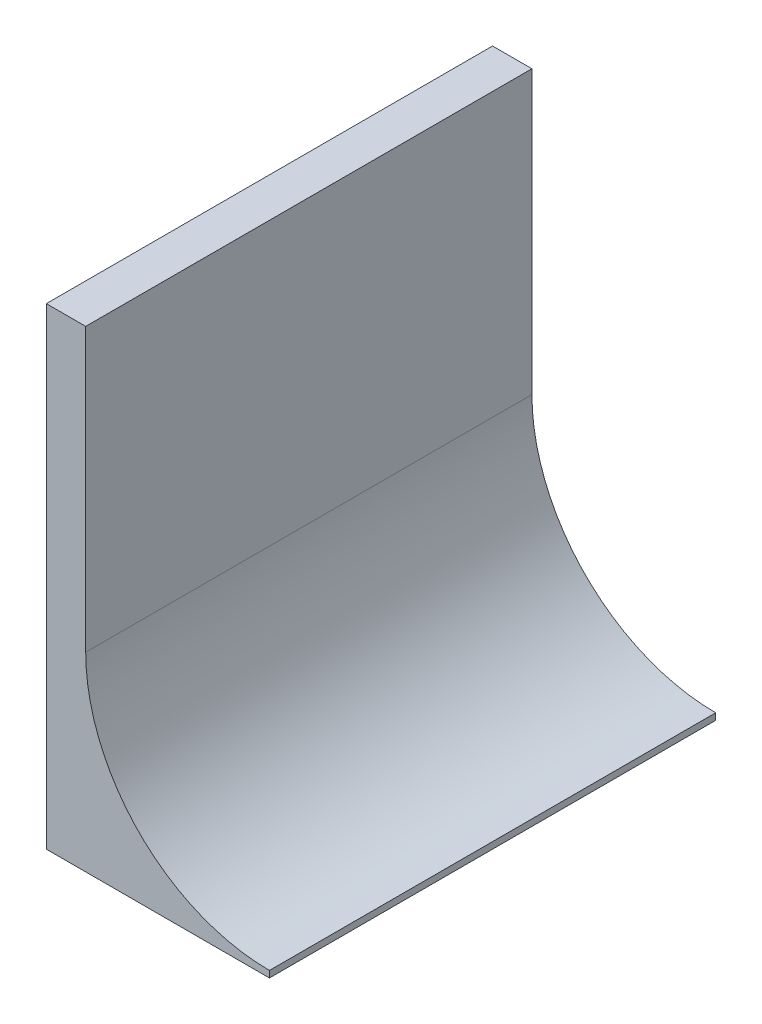
SolidWorks part; units mm, degrees
ref_plane "Front Plane" through (0, 0, 0) normal (0, 0, 1) x (1, 0, 0)
ref_plane "Top Plane" through (0, 0, 0) normal (0, 1, 0) x (1, 0, 0)
ref_plane "Right Plane" through (0, 0, 0) normal (1, 0, 0) x (0, 0, -1)
sketch "Sketch1" plane through (-316.496, -92.2399, -225.3712) normal (1, 0, 0) x (0, 0, -1)
  line L5 (-333.3212, 231.9399) -> (-117.4212, 231.9399)
  line L6 (-333.3212, 231.9399) -> (-333.3212, -47.4601)
  line L7 (-333.3212, -47.4601) -> (-117.4212, -47.4601)
  line L8 (-117.4212, 231.9399) -> (-117.4212, -47.4601)
  line L9 (-333.3212, 231.9399) -> (-117.4212, -47.4601) construction
  line L10 (-333.3212, -47.4601) -> (-117.4212, 231.9399) construction
  point P0 (-225.3712, 92.2399)
  dimension "D1" = 215.9
  dimension "D2" = 279.4
extrude "Boss-Extrude1" add sketch "Sketch1" along normal mid plane 127
sketch "Sketch2" plane through (0, 0, 107.95) normal (0, 0, 1) x (1, 0, 0)
  line L0 (-272.046, -139.7) -> (-252.996, -139.7)
  line L1 (-252.996, -139.7) -> (-252.996, 139.7)
  line L4 (-252.996, 139.7) -> (-379.996, 139.7) construction
  line L9 (-252.996, 139.7) -> (-252.996, -139.7) construction
  line L10 (-252.996, -139.7) -> (-379.996, -139.7) construction
  line L11 (-272.046, -136.525) -> (-272.046, -139.7)
  line L12 (-252.996, 139.7) -> (-379.996, 139.7)
  line L13 (-379.996, 139.7) -> (-379.996, 88.9)
  line L14 (-379.996, 139.7) -> (-379.996, -139.7) construction
  line L15 (-379.996, 88.9) -> (-360.946, 88.9)
  line L16 (-360.946, 88.9) -> (-360.946, -47.625)
  circle A2 centre (-272.046, -47.625) radius 88.9 construction
  arc A3 (-360.946, -47.625) -> (-272.046, -136.525) centre (-272.046, -47.625) ccw
  point P27 (0, 0)
  point P28 (0, 0)
  point P29 (0, 0)
  dimension "D1" = 88.9
  dimension "D2" = 3.175
extrude "Cut-Extrude2" cut sketch "Sketch2" against normal through all
equation "\"ShaftDistance\" = 2.5in"
equation "\"SpokeDistance\" = 1.75in"
equation "\"D_Bearing\" = 7 / 8in"
equation "\"NumShaft\" = 3"
equation "\"Tol_Bearing\" = 0.05in"
equation "\"BearingHole\" = \"D_Bearing\"+\"Tol_Bearing\""
equation "\"IntakeOpening\" = \"SpokeDistance\"+1.75in"
equation "\"SpokeLength\" = 2in"
equation "\"D1@Sketch2\"=\"IntakeOpening\""
